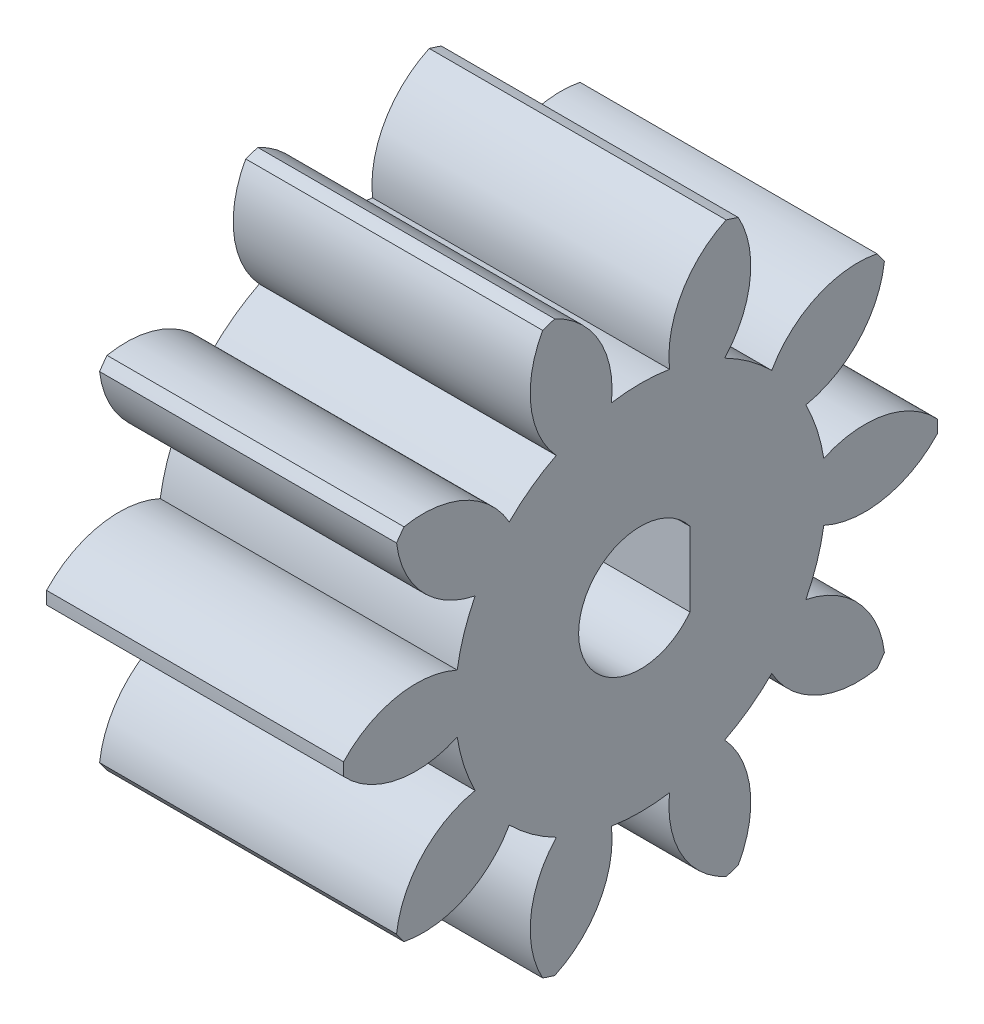
SolidWorks part; units mm, degrees
ref_plane "Front Plane" through (0, 0, 0) normal (0, 0, 1) x (1, 0, 0)
ref_plane "Top Plane" through (0, 0, 0) normal (0, 1, 0) x (1, 0, 0)
ref_plane "Right Plane" through (0, 0, 0) normal (1, 0, 0) x (0, 0, -1)
ref_plane "Plane1" through (4.1778, 0, 0) normal (1, 0, 0) x (0, 0, -1)
sketch "Sketch1" plane through (4.1778, 0, 0) normal (1, 0, 0) x (0, 0, -1)
  circle A0 centre (-6.8257, 0.6053) radius 2.5
  arc A1 (5.1716, 0.8622) -> (0.5811, 1.7778) centre (2.2418, -1.8612) ccw
  arc A2 (0.5811, 1.7778) -> (-0.1442, 4.0103) centre (-6.8257, 0.6053) ccw
  arc A3 (-0.1442, 4.0103) -> (3.0313, 7.4493) centre (-0.9396, 7.9304) ccw
  arc A4 (3.0313, 7.4493) -> (2.7293, 7.8649) centre (-6.8257, 0.6053) ccw
  arc A5 (2.7293, 7.8649) -> (-1.5227, 5.9075) centre (1.9598, 3.9396) ccw
  arc A6 (-1.5227, 5.9075) -> (-3.4217, 7.2872) centre (-6.8257, 0.6053) ccw
  arc A7 (-3.4217, 7.2872) -> (-2.874, 11.936) centre (-6.3694, 9.9911) ccw
  arc A8 (-2.874, 11.936) -> (-3.3626, 12.0947) centre (-6.8257, 0.6053) ccw
  arc A9 (-3.3626, 12.0947) -> (-5.652, 8.0119) centre (-1.6779, 8.4668) ccw
  arc A10 (-5.652, 8.0119) -> (-7.9993, 8.0119) centre (-6.8257, 0.6053) ccw
  arc A11 (-7.9993, 8.0119) -> (-10.2887, 12.0947) centre (-11.9734, 8.4668) ccw
  arc A12 (-10.2887, 12.0947) -> (-10.7773, 11.936) centre (-6.8257, 0.6053) ccw
  arc A13 (-10.7773, 11.936) -> (-10.2296, 7.2872) centre (-7.2819, 9.9911) ccw
  arc A14 (-10.2296, 7.2872) -> (-12.1286, 5.9075) centre (-6.8257, 0.6053) ccw
  arc A15 (-12.1286, 5.9075) -> (-16.3806, 7.8649) centre (-15.6111, 3.9396) ccw
  arc A16 (-16.3806, 7.8649) -> (-16.6826, 7.4493) centre (-6.8257, 0.6053) ccw
  arc A17 (-16.6826, 7.4493) -> (-13.5071, 4.0103) centre (-12.7117, 7.9304) ccw
  arc A18 (-13.5071, 4.0103) -> (-14.2324, 1.7778) centre (-6.8257, 0.6053) ccw
  arc A19 (-14.2324, 1.7778) -> (-18.8229, 0.8622) centre (-15.8931, -1.8612) ccw
  arc A20 (-18.8229, 0.8622) -> (-18.8229, 0.3484) centre (-6.8257, 0.6053) ccw
  arc A21 (-18.8229, 0.3484) -> (-14.2324, -0.5673) centre (-15.8931, 3.0717) ccw
  arc A22 (-14.2324, -0.5673) -> (-13.5071, -2.7997) centre (-6.8257, 0.6053) ccw
  arc A23 (-13.5071, -2.7997) -> (-16.6826, -6.2387) centre (-12.7117, -6.7198) ccw
  arc A24 (-16.6826, -6.2387) -> (-16.3806, -6.6544) centre (-6.8257, 0.6053) ccw
  arc A25 (-16.3806, -6.6544) -> (-12.1286, -4.6969) centre (-15.6111, -2.7291) ccw
  arc A26 (-12.1286, -4.6969) -> (-10.2296, -6.0766) centre (-6.8257, 0.6053) ccw
  arc A27 (-10.2296, -6.0766) -> (-10.7773, -10.7254) centre (-7.2819, -8.7806) ccw
  arc A28 (-10.7773, -10.7254) -> (-10.2887, -10.8842) centre (-6.8257, 0.6053) ccw
  arc A29 (-10.2887, -10.8842) -> (-7.9993, -6.8013) centre (-11.9734, -7.2562) ccw
  arc A30 (-7.9993, -6.8013) -> (-5.652, -6.8013) centre (-6.8257, 0.6053) ccw
  arc A31 (-5.652, -6.8013) -> (-3.3626, -10.8842) centre (-1.6779, -7.2562) ccw
  arc A32 (-3.3626, -10.8842) -> (-2.874, -10.7254) centre (-6.8257, 0.6053) ccw
  arc A33 (-2.874, -10.7254) -> (-3.4217, -6.0766) centre (-6.3694, -8.7806) ccw
  arc A34 (-3.4217, -6.0766) -> (-1.5227, -4.6969) centre (-6.8257, 0.6053) ccw
  arc A35 (-1.5227, -4.6969) -> (2.7293, -6.6544) centre (1.9598, -2.7291) ccw
  arc A36 (2.7293, -6.6544) -> (3.0313, -6.2387) centre (-6.8257, 0.6053) ccw
  arc A37 (3.0313, -6.2387) -> (-0.1442, -2.7997) centre (-0.9396, -6.7198) ccw
  arc A38 (-0.1442, -2.7997) -> (0.5811, -0.5673) centre (-6.8257, 0.6053) ccw
  arc A39 (0.5811, -0.5673) -> (5.1716, 0.3484) centre (2.2418, 3.0717) ccw
  arc A40 (5.1716, 0.3484) -> (5.1716, 0.8622) centre (-6.8257, 0.6053) ccw
extrude "Boss-Extrude1" add sketch "Sketch1" against normal blind 12
sketch "Sketch2" plane through (4.1778, 0, 0) normal (1, 0, 0) x (0, 0, -1)
  line L0 (-4.8257, 3.6172) -> (-4.8257, -3.2287)
  circle A0 centre (-6.8257, 0.6053) radius 2.5 construction
  circle A1 centre (-6.8257, 0.6053) radius 2.5
  circle M3 centre (-6.8257, 0.6053) radius 2.5
  dimension "D1" = 4.5
extrude "Boss-Extrude2" add sketch "Sketch2" against normal up to surface (12 mm away) contours L0 M3
